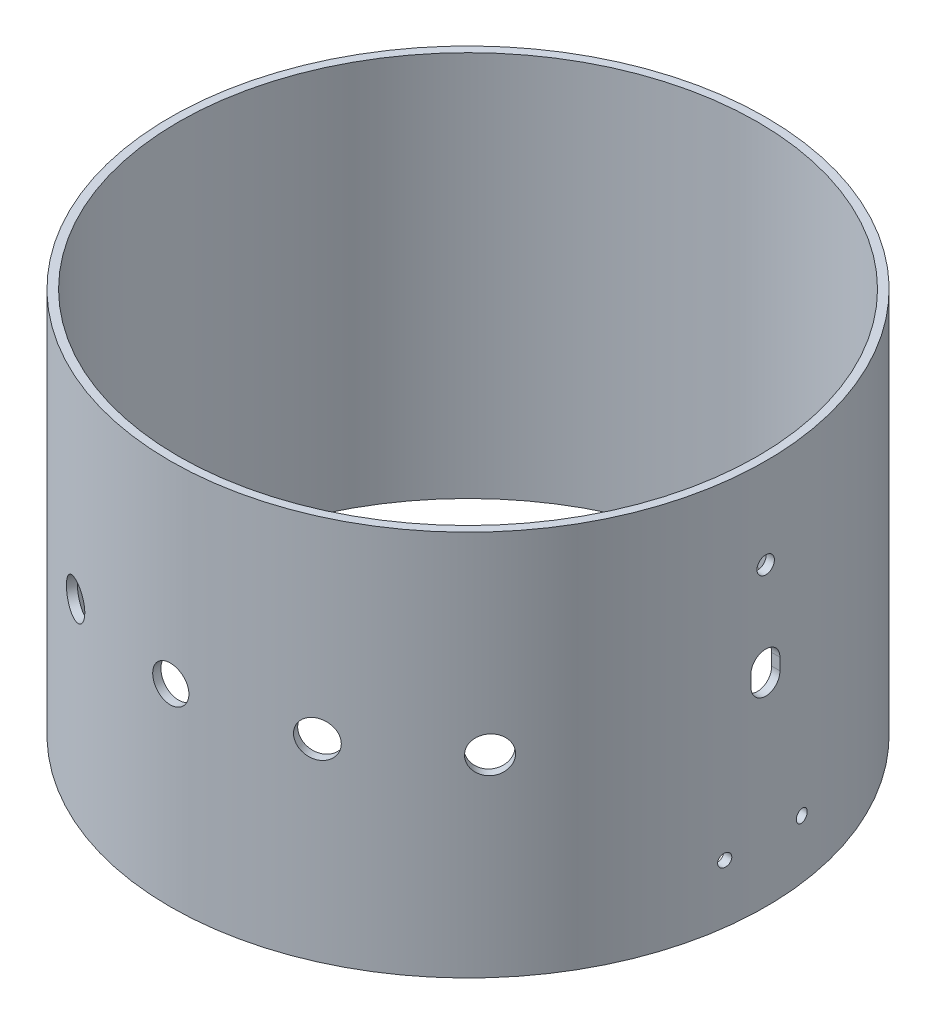
SolidWorks part; units mm, degrees
material "C-Glass Fiber"
ref_plane "Front Plane" through (0, 0, 0) normal (0, 0, 1) x (1, 0, 0)
ref_plane "Top Plane" through (0, 0, 0) normal (0, 1, 0) x (1, 0, 0)
ref_plane "Right Plane" through (0, 0, 0) normal (1, 0, 0) x (0, 0, -1)
sketch "Body Tube Profile" plane through (0, 0, 0) normal (0, 1, 0) x (1, 0, 0)
  circle A0 centre (0, 0) radius 76.2
  circle A1 centre (0, 0) radius 78.359
  dimension "D1" = 152.4
  dimension "D2" = 156.718
extrude "Body Tube Extrustion" add sketch "Body Tube Profile" along normal blind 101.6
ref_plane "Plane1" through (0, 0, 78.359) normal (0, 0, 1) x (1, 0, 0)
sketch "Sketch1" plane through (0, 0, 78.359) normal (0, 0, 1) x (1, 0, 0)
  line L0 (0, 0) -> (0, 101.6) construction
  line L1 (78.359, 101.6) -> (-78.359, 101.6) construction
  point P5 (0, 50.8)
hole_wizard "3/8 (0.375) Diameter Hole1" positions "Sketch1" profile "Sketch2" hole size "3/8" standard "ANSI Inch"
sketch "Sketch2" plane through (0, 50.8, 78.359) normal (1, 0, 0) x (0, -1, 0)
  line L0 (0, 0) -> (0, 2.159)
  line L1 (0, 2.159) -> (4.7625, 2.159)
  line L2 (4.7625, 2.159) -> (4.7625, 0)
  line L5 (4.7625, 0) -> (0, 0)
  line L11 (0, -6.35) -> (0, 107.95) construction
  dimension "Thru Hole Dia." = 9.525
  dimension "Thru Hole Depth" = 2.159
pattern_circular "CirPattern1" count 3 every 24 about axis through (0, 101.6, 0) along (0, 1, 0) of "3/8 (0.375) Diameter Hole1"
ref_plane "Plane2" through (78.359, 0, 0) normal (1, 0, 0) x (0, 0, -1)
sketch "Sketch4" plane through (78.359, 0, 0) normal (1, 0, 0) x (0, 0, -1)
  line L0 (0, 101.6) -> (0, 0) construction
  line L1 (78.359, 101.6) -> (-78.359, 101.6) construction
  line L5 (-16.24, 91.4193) -> (16.24, 91.4193) construction
  line L6 (-16.24, 91.4193) -> (-16.24, 10.1807) construction
  line L7 (-16.24, 10.1807) -> (16.24, 10.1807) construction
  line L8 (16.24, 91.4193) -> (16.24, 10.1807) construction
  circle A0 centre (10.1395, 15.368) radius 1.651
  circle A1 centre (-10.1395, 15.368) radius 1.651
  circle A2 centre (0, 77.9499) radius 2.286
  point P5 (-10.1395, 15.368)
  point P6 (10.1395, 15.368)
  point P9 (0, 77.9499)
  dimension "D4" = 3.302
  dimension "D5" = 4.572
  dimension "D1" = 10.1395
  dimension "D2" = 10.1395
  dimension "D3" = 62.5819
  dimension "D6" = 5.1873
  dimension "D7" = 13.4694
  dimension "D8" = 6.1005
  dimension "D9" = 6.1005
  dimension "D10" = 10.1807
extrude "Cut-Extrude1" cut sketch "Sketch4" against normal up to next
sketch "Sketch5" plane through (78.359, 0, 0) normal (1, 0, 0) x (0, 0, -1)
  line L0 (0, 0) -> (0, 101.6) construction
  line L1 (76.2, 101.6) -> (-76.2, 101.6) construction
  line L2 (-3.81, 54.9376) -> (-3.81, 51.834)
  line L3 (3.81, 54.9376) -> (3.81, 51.834)
  line L4 (-10.1395, 15.368) -> (10.1395, 15.368) construction
  circle A0 centre (0, 54.9376) radius 3.81
  circle A1 centre (0, 51.834) radius 3.81
  dimension "D2" = 7.62
  dimension "D1" = 3.1036
  dimension "D3" = 36.466
extrude "Cut-Extrude2" cut sketch "Sketch5" against normal up to next contours L0 A1 A0 | A1 L0 A0 | A0 L0 A1 | L0 A0 A1 | A1 L3 A0 | A1 A0 L2
equation "\"Length\"=4"
equation "\"Outer Diameter\"= 6.17"
equation "\"Inner Diameter\"= 6"
equation "\"Wall Thickness\"= 0.085"
equation "\"D1@Body Tube Profile\" = \"Inner Diameter\""
equation "\"D2@Body Tube Profile\" = \"Outer Diameter\""
equation "\"D1@Body Tube Extrustion\" = \"Length\""
equation "\"Key Hole Dia\"=0.375"
equation "\"Hole Angle 1\"= 15"
equation "\"Hole Angle 2\"= 45"
equation "\"D10@Sketch4\"=(4-3.19837298)/2"
